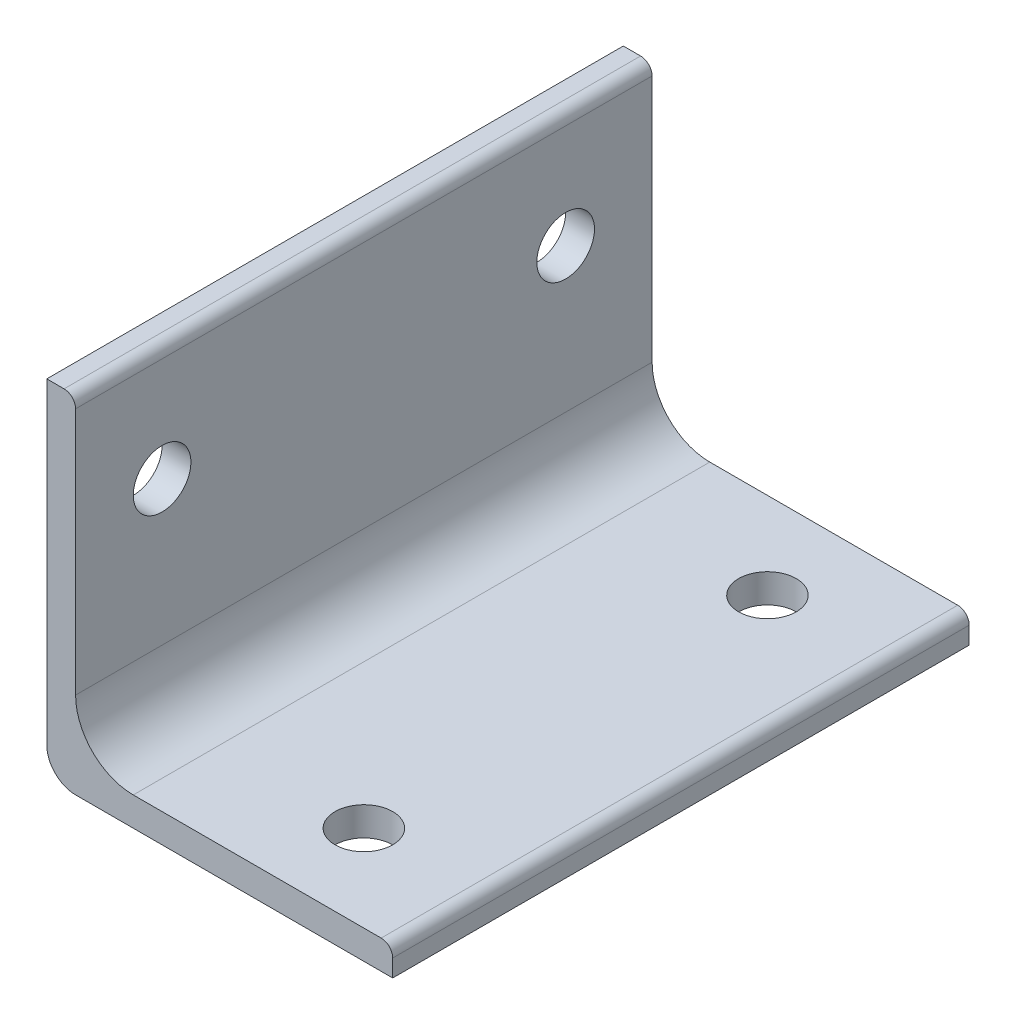
SolidWorks part; units mm, degrees
material "Plain Carbon Steel"
ref_plane "Front" through (0, 0, 0) normal (0, 0, 1) x (1, 0, 0)
ref_plane "Top" through (0, 0, 0) normal (0, 1, 0) x (1, 0, 0)
ref_plane "Right" through (0, 0, 0) normal (1, 0, 0) x (0, 0, -1)
sketch "Sketch1" plane through (0, 0, 0) normal (0, 0, 1) x (1, 0, 0)
  line L0 (0, 0) -> (0, 34.925)
  line L1 (0, 34.925) -> (-3.175, 34.925)
  line L2 (-3.175, 34.925) -> (-3.175, -3.175)
  line L3 (-3.175, -3.175) -> (34.925, -3.175)
  line L4 (34.925, -3.175) -> (34.925, 0)
  line L5 (34.925, 0) -> (0, 0)
  dimension "Height" = 38.1
  dimension "Width" = 38.1
  dimension "Wall Thickness" = 3.175
sketch "Sketch2" plane through (0, 0, 0) normal (1, 0, 0) x (0, 0, -1)
  line L0 (-152.4, 0) -> (152.4, 0) construction
  line L1 (152.4, -3.175) -> (-152.4, -3.175) construction
  point P2 (0, 0)
  point P3 (0, -3.175)
  point P5 (152.4, 0)
  point P9 (0, -3.175)
  point P10 (-152.4, -3.175)
  point P11 (152.4, -3.175)
  point P12 (-152.4, 0)
  dimension "Length" = 304.8
sketch "Sketch3" plane through (0, 0, 0) normal (0, 0, 1) x (1, 0, 0)
  line L0 (0, 0) -> (0, 34.925) construction
  line L1 (0, 34.925) -> (-3.175, 34.925) construction
  line L2 (-3.175, 34.925) -> (-3.175, -3.175) construction
  line L3 (-3.175, -3.175) -> (34.925, -3.175) construction
  line L4 (34.925, -3.175) -> (34.925, 0) construction
  line L5 (34.925, 0) -> (0, 0) construction
  line L6 (0, 6.35) -> (0, 33.655)
  line L7 (-1.27, 34.925) -> (-3.175, 34.925)
  line L8 (-3.175, 34.925) -> (-3.175, 0)
  line L9 (0, -3.175) -> (34.925, -3.175)
  line L10 (34.925, -3.175) -> (34.925, -1.27)
  line L11 (33.655, 0) -> (6.35, 0)
  arc A0 (0, 6.35) -> (6.35, 0) centre (6.35, 6.35) ccw
  arc A1 (34.925, -1.27) -> (33.655, 0) centre (33.655, -1.27) ccw
  arc A2 (0, 33.655) -> (-1.27, 34.925) centre (-1.27, 33.655) ccw
  arc A3 (-3.175, 0) -> (0, -3.175) centre (0, 0) ccw
  dimension "D1" = 1.27
  dimension "D2" = 6.35
extrude "Boss-Extrude1" add sketch "Sketch3" along normal blind 63.5
hole_wizard "1/4 (0.25) Diameter Hole1" positions "3DSketch1" profile "Sketch4" hole size "1/4" standard "ANSI Inch" end condition through all
sketch3d "3DSketch1"
  line L0 (33.655, 0, 63.5) -> (6.35, 0, 63.5) construction
  line L1 (33.655, 0, 0) -> (6.35, 0, 0) construction
  line L2 (33.655, 0, 63.5) -> (33.655, 0, 0) construction
  line L3 (0, 33.655, 63.5) -> (0, 33.655, 0) construction
  line L4 (0, 6.35, 63.5) -> (0, 33.655, 63.5) construction
  line L5 (0, 6.35, 0) -> (0, 33.655, 0) construction
  point P0 (22.225, 0, 53.975)
  point P2 (22.225, 0, 9.525)
  point P4 (0, 22.225, 9.525)
  point P6 (0, 22.225, 53.975)
  dimension "D1" = 9.525
  dimension "D2" = 9.525
  dimension "D3" = 11.43
  dimension "D4" = 11.43
  dimension "D5" = 9.525
  dimension "D6" = 9.525
sketch "Sketch4" plane through (22.225, 0, 53.975) normal (1, 0, 0) x (0, 0, 1)
  line L0 (0, 0) -> (0, 3.175)
  line L1 (0, 3.175) -> (3.175, 3.175)
  line L2 (3.175, 3.175) -> (3.175, 0)
  line L5 (3.175, 0) -> (0, 0)
  line L11 (0, -6.35) -> (0, 107.95) construction
  dimension "Thru Hole Dia." = 6.35
  dimension "Thru Hole Depth" = 3.175
equation "\"D1@Sketch3\"=\"Wall Thickness@Sketch1\"*0.4"
equation "\"D2@Sketch3\"=\"Wall Thickness@Sketch1\"*2"
